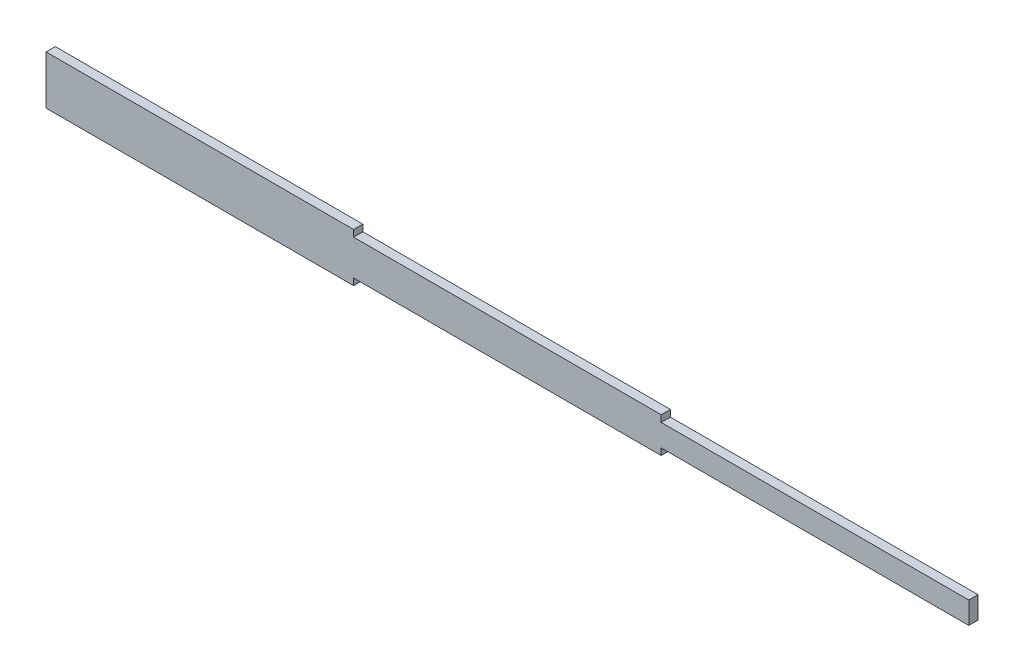
SolidWorks part; units mm, degrees
ref_plane "Front Plane" through (0, 0, 0) normal (0, 0, 1) x (1, 0, 0)
ref_plane "Top Plane" through (0, 0, 0) normal (0, 1, 0) x (1, 0, 0)
ref_plane "Right Plane" through (0, 0, 0) normal (1, 0, 0) x (0, 0, -1)
sketch "Sketch1" plane through (0, 0, 0) normal (1, 0, 0) x (0, 0, -1)
  line L5 (-15, -79.125) -> (15, -79.125)
  line L6 (-15, -79.125) -> (-15, 79.125)
  line L7 (-15, 79.125) -> (15, 79.125)
  line L8 (15, -79.125) -> (15, 79.125)
  line L9 (-15, -79.125) -> (15, 79.125) construction
  line L10 (-15, 79.125) -> (15, -79.125) construction
  point P0 (0, 0)
  point P1 (0, 0)
  point P6 (0, 0)
  point P8 (0, 0)
  dimension "D1" = 30
  dimension "D2" = 158.25
extrude "Boss-Extrude1" add sketch "Sketch1" along normal blind 1000
sketch "Sketch3" plane through (1000, 0, 0) normal (1, 0, 0) x (0, 0, -1)
  line L0 (15, -79.125) -> (15, 79.125) construction
  line L1 (-15, -57.475) -> (15, -57.475)
  line L2 (-15, -57.475) -> (-15, 57.475)
  line L3 (-15, 57.475) -> (15, 57.475)
  line L4 (15, -57.475) -> (15, 57.475)
  line L5 (-15, -57.475) -> (15, 57.475) construction
  line L6 (-15, 57.475) -> (15, -57.475) construction
  point P0 (0, 0)
  dimension "D1" = 30
  dimension "D2" = 114.95
extrude "Boss-Extrude2" add sketch "Sketch3" along normal blind 1000
sketch "Sketch4" plane through (2000, 0, 0) normal (1, 0, 0) x (0, 0, -1)
  line L0 (15, -57.475) -> (15, 57.475) construction
  line L1 (-15, -35.825) -> (15, -35.825)
  line L2 (-15, -35.825) -> (-15, 35.825)
  line L3 (-15, 35.825) -> (15, 35.825)
  line L4 (15, -35.825) -> (15, 35.825)
  line L5 (-15, -35.825) -> (15, 35.825) construction
  line L6 (-15, 35.825) -> (15, -35.825) construction
  point P0 (0, 0)
  dimension "D1" = 30
  dimension "D2" = 71.65
extrude "Boss-Extrude3" add sketch "Sketch4" along normal blind 1000
sketch "Sketch5" plane through (0, 0, 0) normal (-1, 0, 0) x (0, 0, 1)
  line L0 (-15, 79.125) -> (15, 79.125) construction
  line L1 (-13, -77.125) -> (13, -77.125)
  line L2 (-13, -77.125) -> (-13, 77.125)
  line L3 (-13, 77.125) -> (13, 77.125)
  line L4 (13, -77.125) -> (13, 77.125)
  line L5 (-13, -77.125) -> (13, 77.125) construction
  line L6 (-13, 77.125) -> (13, -77.125) construction
  line L7 (-15, -79.125) -> (-15, 79.125) construction
  point P0 (0, 0)
  dimension "D1" = 2
  dimension "D2" = 2
extrude "Cut-Extrude1" cut sketch "Sketch5" against normal blind 998
sketch "Sketch6" plane through (998, 0, 0) normal (-1, 0, 0) x (0, 0, 1)
  line L0 (-15, 57.475) -> (15, 57.475) construction
  line L1 (13, -55.475) -> (-13, -55.475)
  line L2 (13, -55.475) -> (13, 55.475)
  line L3 (13, 55.475) -> (-13, 55.475)
  line L4 (-13, -55.475) -> (-13, 55.475)
  line L5 (13, -55.475) -> (-13, 55.475) construction
  line L6 (13, 55.475) -> (-13, -55.475) construction
  line L7 (15, 79.125) -> (15, -79.125) construction
  point P0 (0, 0)
  point P8 (0, 57.475)
  dimension "D1" = 2
  dimension "D2" = 2
extrude "Cut-Extrude2" cut sketch "Sketch6" against normal blind 998
sketch "Sketch7" plane through (1996, 0, 0) normal (-1, 0, 0) x (0, 0, 1)
  line L0 (13, -55.475) -> (13, 55.475) construction
  line L1 (-13, -33.825) -> (13, -33.825)
  line L2 (-13, -33.825) -> (-13, 33.825)
  line L3 (-13, 33.825) -> (13, 33.825)
  line L4 (13, -33.825) -> (13, 33.825)
  line L5 (-13, -33.825) -> (13, 33.825) construction
  line L6 (-13, 33.825) -> (13, -33.825) construction
  line L7 (-15, 35.825) -> (15, 35.825) construction
  line L8 (-15, 35.825) -> (-15, 57.475) construction
  point P0 (0, 0)
  dimension "D1" = 2
  dimension "D2" = 2
extrude "Cut-Extrude3" cut sketch "Sketch7" against normal blind 998
